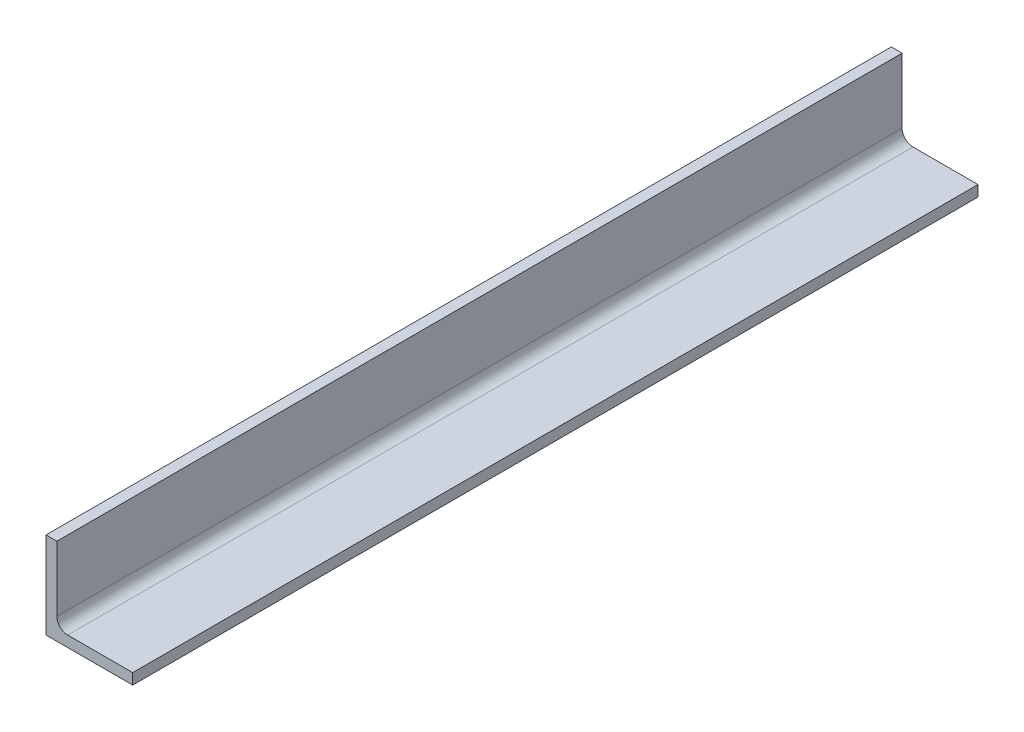
SolidWorks part; units mm, degrees
ref_plane "Front Plane" through (0, 0, 0) normal (0, 0, 1) x (1, 0, 0)
ref_plane "Top Plane" through (0, 0, 0) normal (0, 1, 0) x (1, 0, 0)
ref_plane "Right Plane" through (0, 0, 0) normal (1, 0, 0) x (0, 0, -1)
sketch "Sketch1" plane through (0, 0, 0) normal (0, 0, 1) x (1, 0, 0)
  line L0 (0, 25.4) -> (0, 0)
  line L1 (0, 0) -> (25.4, 0)
  line L2 (25.4, 0) -> (25.4, 3.175)
  line L3 (25.4, 3.175) -> (3.175, 3.175)
  line L4 (3.175, 3.175) -> (3.175, 25.4)
  line L5 (3.175, 25.4) -> (0, 25.4)
  dimension "D1" = 25.4
  dimension "D2" = 3.175
extrude "Boss-Extrude1" add sketch "Sketch1" along normal mid plane 247.66
fillet "Fillet1" radius 3.175 1 edges at (3.175, 3.175, 0)
